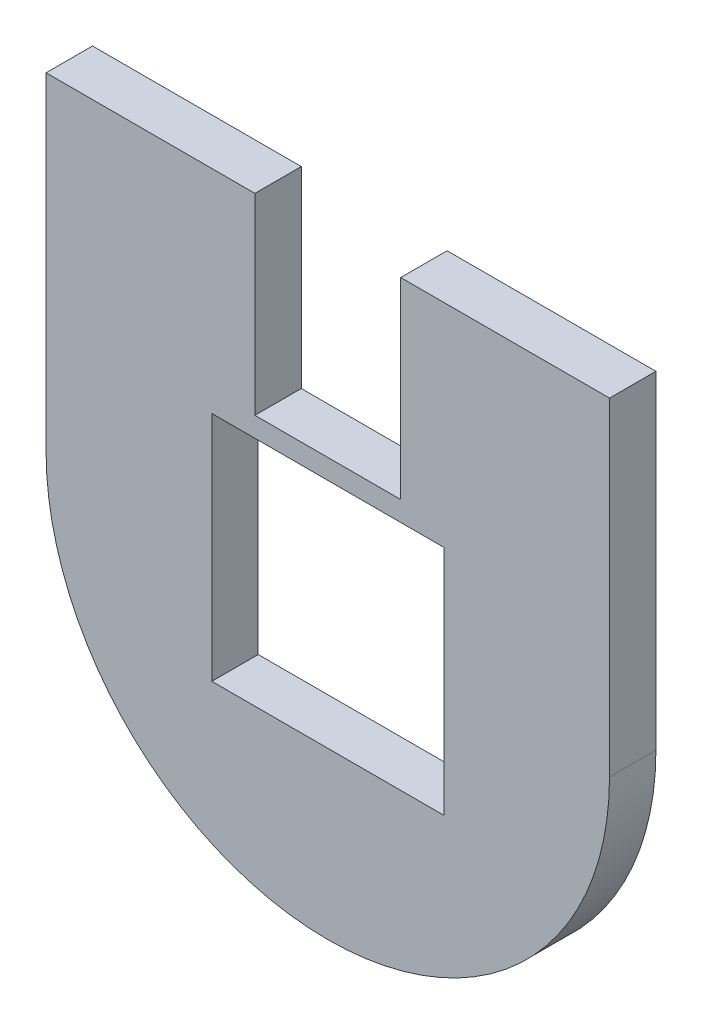
SolidWorks part; units mm, degrees
ref_plane "Front Plane" through (0, 0, 0) normal (0, 0, 1) x (1, 0, 0)
ref_plane "Top Plane" through (0, 0, 0) normal (0, 1, 0) x (1, 0, 0)
ref_plane "Right Plane" through (0, 0, 0) normal (1, 0, 0) x (0, 0, -1)
sketch "Sketch1" plane through (0, 0, 0) normal (0, 0, 1) x (1, 0, 0)
  line L1 (0, 0) -> (85, 0)
  line L2 (0, 0) -> (0, 95)
  line L3 (0, 95) -> (85, 95)
  line L4 (85, 0) -> (85, 95)
  dimension "D1" = 95
  dimension "D2" = 85
extrude "Boss-Extrude1" add sketch "Sketch1" along normal blind 7
sketch "Sketch2" plane through (0, 0, 7) normal (0, 0, 1) x (1, 0, 0)
  line L0 (0, 0) -> (85, 0) construction
  line L1 (25, 27.5) -> (60, 27.5)
  line L2 (25, 27.5) -> (25, 62.5)
  line L3 (25, 62.5) -> (60, 62.5)
  line L4 (60, 27.5) -> (60, 62.5)
  line L5 (25, 27.5) -> (60, 62.5) construction
  line L6 (25, 62.5) -> (60, 27.5) construction
  point P0 (42.5, 45)
  point P7 (42.5, 0)
  dimension "D1" = 0
  dimension "D2" = 35
  dimension "D3" = 35
  dimension "D4" = 45
extrude "Cut-Extrude1" cut sketch "Sketch2" against normal blind 7
sketch "Sketch4" plane through (0, 95, 0) normal (0, 1, 0) x (1, 0, 0)
  line L0 (0, -3.5) -> (85, -3.5) construction
  line L1 (0, -7) -> (0, 0) construction
  line L2 (85, -7) -> (85, 0) construction
  circle A0 centre (21.25, -3.5) radius 1.5
  circle A1 centre (63.75, -3.5) radius 1.5
  dimension "D1" = 3
  dimension "D2" = 3
  dimension "D3" = 21.25
  dimension "D4" = 21.25
sketch "Sketch6" plane through (0, 0, 0) normal (0, 0, -1) x (-1, 0, 0)
  line L0 (-85, 95) -> (0, 95) construction
  line L1 (-85, 0) -> (-85, 95) construction
  line L2 (-42.5, 62.5) -> (-42.5, 65.8033) construction
  line L3 (-60, 62.5) -> (-25, 62.5) construction
  line L4 (0, 95) -> (0, 0) construction
  line L5 (0, 0) -> (-85, 0) construction
  circle A0 centre (-80.75, 90.75) radius 1.5
  circle A1 centre (-4.25, 90.75) radius 1.5
  circle A2 centre (-4.45, 4.25) radius 1.5
  circle A3 centre (-80.75, 7.25) radius 1.5
  dimension "D1" = 3
  dimension "D5" = 3
  dimension "D7" = 3
  dimension "D2" = 4.25
  dimension "D3" = 4.25
  dimension "D4" = 4.45
  dimension "D6" = 4.25
  dimension "D8" = 7.25
  dimension "D9" = 4.25
sketch "Sketch7" plane through (0, 0, 0) normal (0, 0, -1) x (-1, 0, 0)
  line L0 (-85, 45) -> (-85, 0)
  line L1 (-85, 0) -> (0, 0)
  line L2 (0, 0) -> (0, 45)
  arc A0 (-85, 45) -> (0, 45) centre (-42.5, 45) ccw
  dimension "D1" = 85
extrude "Cut-Extrude4" cut sketch "Sketch7" against normal blind 10
sketch "Sketch8" plane through (0, 0, 7) normal (0, 0, 1) x (1, 0, 0)
  line L0 (85, 95) -> (0, 95) construction
  line L1 (85, 45) -> (85, 95) construction
  line L2 (42.5, 62.5) -> (42.5, 67.7032) construction
  line L3 (60, 62.5) -> (25, 62.5) construction
  circle A0 centre (80.75, 63) radius 1.5
  circle A1 centre (4.25, 63) radius 1.5
  dimension "D1" = 3
  dimension "D2" = 32
  dimension "D3" = 4.25
sketch "Sketch10" plane through (0, 0, 0) normal (0, 0, -1) x (-1, 0, 0)
  line L0 (-42.5, 2.5) -> (-42.5, 26.8409) construction
  arc A0 (-85, 45) -> (0, 45) centre (-42.5, 45) ccw construction
  circle A1 centre (-42.5, 6.75) radius 1.5
  dimension "D1" = 3
  dimension "D2" = 4.25
sketch "Sketch11" plane through (0, 0, 7) normal (0, 0, 1) x (1, 0, 0)
  circle A0 centre (42.5, 6.75) radius 1.5 construction
  circle A1 centre (42.5, 6.75) radius 1.5
sketch "Sketch12" plane through (0, 0, 0) normal (0, 0, -1) x (-1, 0, 0)
  line L0 (-85, 95) -> (0, 95) construction
  line L1 (-53.5, 95) -> (-31.5, 95)
  line L2 (-60, 62.5) -> (-25, 62.5) construction
  line L3 (-53.5, 95) -> (-31.5, 95)
  line L4 (-53.5, 95) -> (-53.5, 65.5)
  line L5 (-53.5, 65.5) -> (-31.5, 65.5)
  line L6 (-31.5, 95) -> (-31.5, 65.5)
  point P0 (-42.5, 95)
  point P6 (-42.5, 95)
  line M17 (0, 95) -> (-85, 95)
  dimension "D1" = 22
  dimension "D2" = 0
  dimension "D3" = 3
extrude "Cut-Extrude9" cut sketch "Sketch12" against normal blind 10 contours L6 L4 L5 M17
sketch "Sketch13" plane through (0, 95, 0) normal (0, 1, 0) x (1, 0, 0)
  line L1 (0, 0) -> (31.5, 0)
  line L2 (0, 0) -> (0, -7)
  line L3 (0, -7) -> (31.5, -7)
  line L4 (31.5, 0) -> (31.5, -7)
  line L5 (53.5, 0) -> (85, 0)
  line L6 (53.5, 0) -> (53.5, -7)
  line L7 (53.5, -7) -> (85, -7)
  line L8 (85, 0) -> (85, -7)
extrude "Cut-Extrude10" cut sketch "Sketch13" against normal blind 0.5
